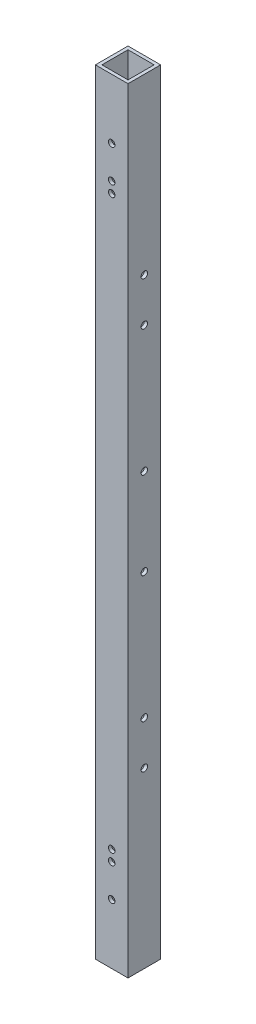
SolidWorks part; units mm, degrees
material "6061 Alloy"
ref_plane "Front Plane" through (0, 0, 0) normal (0, 0, 1) x (1, 0, 0)
ref_plane "Top Plane" through (0, 0, 0) normal (0, 1, 0) x (1, 0, 0)
ref_plane "Right Plane" through (0, 0, 0) normal (1, 0, 0) x (0, 0, -1)
sketch "Sketch1" plane through (0, 0, 0) normal (0, 1, 0) x (1, 0, 0)
  line L1 (0, 0) -> (15, 0)
  line L2 (0, 0) -> (0, 15)
  line L3 (0, 15) -> (15, 15)
  line L4 (15, 0) -> (15, 15)
  dimension "D1" = 15
extrude "Extrude-Thin1" add sketch "Sketch1" along normal blind 356 thin thin type one direction reverse wall 1.5
sketch "Sketch2"
  line L0 (7.5, 0) -> (7.5, 356) construction
  line L1 (0, 0) -> (15, 0) construction
  line L2 (0, 356) -> (15, 356) construction
  line L3 (15, 356) -> (15, 0) construction
  line L4 (13.5, 178) -> (1.5, 178) construction
  line L5 (13.5, 356) -> (13.5, 0) construction
  line L6 (1.5, 356) -> (1.5, 0) construction
  circle A0 centre (7.5, 27.5) radius 1.5
  circle A1 centre (7.5, 47.5) radius 1.5
  circle A4 centre (7.5, 42.5) radius 1.5
  circle A6 centre (7.5, 328.5) radius 1.5
  circle A7 centre (7.5, 313.5) radius 1.5
  circle A8 centre (7.5, 308.5) radius 1.5
other "AlignGroup1" parameters "D1"=8.8486, "D2"=0, "D3"=0, "D4"=27.5, "D5"=42.5, "D6"=47.5, "D7"=300.5, "D8"=305.5, "D9"=320.5
other "AlignGroup2"
extrude "Cut-Extrude1" cut sketch "Sketch2" against normal through all
sketch "Sketch3" plane through (15, 0, 0) normal (1, 0, 0) x (0, 0, -1)
  line L2 (0, 0) -> (15, 0) construction
  line L3 (15, 356) -> (15, 0) construction
  circle A6 centre (7.5, 276.148) radius 1.5
  circle A7 centre (7.5, 256.148) radius 1.5
  circle A8 centre (7.5, 198) radius 1.5
  circle A9 centre (7.5, 158) radius 1.5
  circle A10 centre (7.5, 99.852) radius 1.5
  circle A11 centre (7.5, 79.852) radius 1.5
  dimension "D1" = 3
  dimension "D2" = 7.5
  dimension "D3" = 79.852
  dimension "D4" = 99.852
  dimension "D5" = 158
  dimension "D6" = 198
  dimension "D7" = 256.148
  dimension "D8" = 276.148
other "AlignGroup3"
other "AlignGroup4"
extrude "Cut-Extrude2" cut sketch "Sketch3" against normal through all
